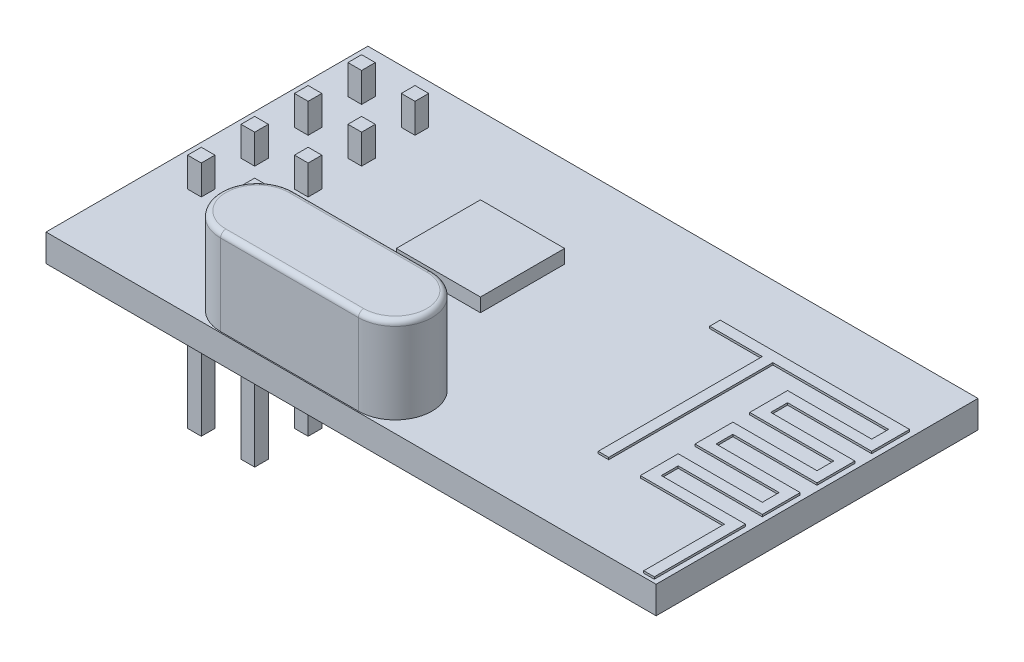
SolidWorks part; units mm, degrees
ref_plane "Front Plane" through (0, 0, 0) normal (0, 0, 1) x (1, 0, 0)
ref_plane "Top Plane" through (0, 0, 0) normal (0, 1, 0) x (1, 0, 0)
ref_plane "Right Plane" through (0, 0, 0) normal (1, 0, 0) x (0, 0, -1)
sketch "Sketch1" plane through (0, 0, 0) normal (0, 1, 0) x (1, 0, 0)
  line L1 (-15.0564, 7.1753) -> (13.9436, 7.1753)
  line L2 (-15.0564, 7.1753) -> (-15.0564, -8.1247)
  line L3 (-15.0564, -8.1247) -> (13.9436, -8.1247)
  line L4 (13.9436, 7.1753) -> (13.9436, -8.1247)
  dimension "D1" = 15.3
  dimension "D2" = 29
extrude "Boss-Extrude1" add sketch "Sketch1" along normal blind 1.3
sketch "Sketch2" plane through (0, 1.3, 0) normal (0, 1, 0) x (1, 0, 0)
  line L0 (-6.8064, -6.3247) -> (-0.2564, -6.3247) construction
  line L1 (-6.8064, -4.5747) -> (-0.2564, -4.5747)
  line L2 (-6.8064, -8.0747) -> (-0.2564, -8.0747)
  line L3 (-15.0564, 7.1753) -> (-15.0564, -8.1247) construction
  line L4 (-15.0564, -8.1247) -> (13.9436, -8.1247) construction
  arc A0 (-6.8064, -4.5747) -> (-6.8064, -8.0747) centre (-6.8064, -6.3247) ccw
  arc A1 (-0.2564, -8.0747) -> (-0.2564, -4.5747) centre (-0.2564, -6.3247) ccw
  point P2 (-3.5314, -6.3247)
  dimension "D1" = 3.5
  dimension "D2" = 6.55
  dimension "D3" = 8.25
  dimension "D4" = 1.8
extrude "Boss-Extrude2" add sketch "Sketch2" along normal blind 4.1
sketch "Sketch3" plane through (0, 1.3, 0) normal (0, 1, 0) x (1, 0, 0)
  line L0 (-15.0564, 7.1753) -> (-15.0564, -8.1247) construction
  line L1 (-13.4564, 5.2753) -> (-12.8064, 5.2753)
  line L2 (-13.4564, 5.2753) -> (-13.4564, 4.6253)
  line L3 (-13.4564, 4.6253) -> (-12.8064, 4.6253)
  line L4 (-12.8064, 5.2753) -> (-12.8064, 4.6253)
  line L5 (13.9436, 7.1753) -> (-15.0564, 7.1753) construction
  line L6 (-10.9164, 5.2753) -> (-10.9164, 4.6253)
  line L7 (-10.9164, 5.2753) -> (-10.2664, 5.2753)
  line L8 (-10.2664, 5.2753) -> (-10.2664, 4.6253)
  line L9 (-10.9164, 4.6253) -> (-10.2664, 4.6253)
  line L10 (-10.9164, 2.7353) -> (-10.9164, 2.0853)
  line L11 (-10.9164, 2.7353) -> (-10.2664, 2.7353)
  line L12 (-10.2664, 2.7353) -> (-10.2664, 2.0853)
  line L13 (-10.9164, 2.0853) -> (-10.2664, 2.0853)
  line L14 (-10.9164, 0.1953) -> (-10.9164, -0.4547)
  line L15 (-10.9164, 0.1953) -> (-10.2664, 0.1953)
  line L16 (-10.2664, 0.1953) -> (-10.2664, -0.4547)
  line L17 (-10.9164, -0.4547) -> (-10.2664, -0.4547)
  line L18 (-10.9164, -2.3447) -> (-10.9164, -2.9947)
  line L19 (-10.9164, -2.3447) -> (-10.2664, -2.3447)
  line L20 (-10.2664, -2.3447) -> (-10.2664, -2.9947)
  line L21 (-10.9164, -2.9947) -> (-10.2664, -2.9947)
  line L22 (-13.4564, 2.7353) -> (-13.4564, 2.0853)
  line L23 (-13.4564, 2.7353) -> (-12.8064, 2.7353)
  line L24 (-12.8064, 2.7353) -> (-12.8064, 2.0853)
  line L25 (-13.4564, 2.0853) -> (-12.8064, 2.0853)
  line L26 (-13.4564, 0.1953) -> (-13.4564, -0.4547)
  line L27 (-13.4564, 0.1953) -> (-12.8064, 0.1953)
  line L28 (-12.8064, 0.1953) -> (-12.8064, -0.4547)
  line L29 (-13.4564, -0.4547) -> (-12.8064, -0.4547)
  line L30 (-13.4564, -2.3447) -> (-13.4564, -2.9947)
  line L31 (-13.4564, -2.3447) -> (-12.8064, -2.3447)
  line L32 (-12.8064, -2.3447) -> (-12.8064, -2.9947)
  line L33 (-13.4564, -2.9947) -> (-12.8064, -2.9947)
  dimension "D1" = 0.65
  dimension "D2" = 0.65
  dimension "D3" = 1.6
  dimension "D4" = 1.9
  dimension "D5" = 2
  dimension "D6" = 4
extrude "Boss-Extrude3" add sketch "Sketch3" along normal blind 1.4 and the other way blind 10
sketch "Sketch4" plane through (0, 0, 0) normal (0, -1, 0) x (1, 0, 0)
  line L0 (-13.4564, 2.3447) -> (-13.4564, 2.9947) construction
  line L1 (-14.3564, 3.8947) -> (-9.3664, 3.8947)
  line L2 (-14.3564, 3.8947) -> (-14.3564, -6.1753)
  line L3 (-14.3564, -6.1753) -> (-9.3664, -6.1753)
  line L4 (-9.3664, 3.8947) -> (-9.3664, -6.1753)
  line L5 (-10.2664, 2.9947) -> (-10.2664, 2.3447) construction
  line L6 (-10.9164, 2.9947) -> (-10.2664, 2.9947) construction
  line L7 (-10.2664, -5.2753) -> (-10.9164, -5.2753) construction
  dimension "D1" = 0.9
  dimension "D2" = 0.9
  dimension "D3" = 0.9
  dimension "D4" = 0.9
extrude "Boss-Extrude4" add sketch "Sketch4" along normal blind 2.54
sketch "Sketch5" plane through (0, 1.3, 0) normal (0, 1, 0) x (1, 0, 0)
  line L0 (-15.0564, 7.1753) -> (-15.0564, -8.1247) construction
  line L1 (-5.4064, 2.8753) -> (-1.4064, 2.8753)
  line L2 (-5.4064, 2.8753) -> (-5.4064, -1.1247)
  line L3 (-5.4064, -1.1247) -> (-1.4064, -1.1247)
  line L4 (-1.4064, 2.8753) -> (-1.4064, -1.1247)
  line L5 (13.9436, 7.1753) -> (-15.0564, 7.1753) construction
  dimension "D1" = 4
  dimension "D2" = 4
  dimension "D3" = 9.65
  dimension "D4" = 4.3
extrude "Boss-Extrude5" add sketch "Sketch5" along normal blind 0.65
fillet "Fillet1" radius 0.25 4 edges at (-3.5314, 5.4, 4.5747) (1.4936, 5.4, 6.3247) (-3.5314, 5.4, 8.0747) (-8.5564, 5.4, 6.3247)
chamfer "Chamfer1" distance 0.15 angle 45 32 edges at (-10.9164, -8.7, 2.6697) (-10.5914, -8.7, 2.9947) (-10.2664, -8.7, 2.6697) (-10.5914, -8.7, 2.3447) (-13.4564, -8.7, 2.6697) (-13.1314, -8.7, 2.9947) (-12.8064, -8.7, 2.6697) (-13.1314, -8.7, 2.3447) (-10.9164, -8.7, 0.1297) (-10.5914, -8.7, 0.4547) (-10.2664, -8.7, 0.1297) (-10.5914, -8.7, -0.1953) (-10.9164, -8.7, -2.4103) (-10.5914, -8.7, -2.0853) (-10.2664, -8.7, -2.4103) (-10.5914, -8.7, -2.7353) (-13.4564, -8.7, 0.1297) (-13.1314, -8.7, 0.4547) (-12.8064, -8.7, 0.1297) (-13.1314, -8.7, -0.1953) (-13.4564, -8.7, -2.4103) (-13.1314, -8.7, -2.0853) (-12.8064, -8.7, -2.4103) (-13.1314, -8.7, -2.7353) (-10.9164, -8.7, -4.9503) (-10.5914, -8.7, -4.6253) (-10.2664, -8.7, -4.9503) (-10.5914, -8.7, -5.2753) (-13.1314, -8.7, -4.6253) (-12.8064, -8.7, -4.9503) (-13.1314, -8.7, -5.2753) (-13.4564, -8.7, -4.9503)
sketch "Sketch6" plane through (0, 1.3, 0) normal (0, 1, 0) x (1, 0, 0)
  line L0 (4.6936, 4.1733) -> (13.6936, 4.1733)
  line L1 (13.6936, 4.1733) -> (13.6936, 2.3733)
  line L2 (13.6936, 2.3733) -> (9.6936, 2.3733)
  line L3 (9.6936, 2.3733) -> (9.6936, 1.5733)
  line L4 (9.6936, 1.5733) -> (13.6936, 1.5733)
  line L5 (13.6936, 1.5733) -> (13.6936, -0.2267)
  line L6 (13.6936, -0.2267) -> (9.6936, -0.2267)
  line L7 (9.6936, -0.2267) -> (9.6936, -1.0267)
  line L8 (9.6936, -1.0267) -> (13.6936, -1.0267)
  line L9 (13.6936, -1.0267) -> (13.6936, -2.8267)
  line L10 (13.6936, -2.8267) -> (9.6936, -2.8267)
  line L11 (9.6936, -2.8267) -> (9.6936, -3.6267)
  line L12 (9.6936, -3.6267) -> (13.6936, -3.6267)
  line L13 (13.6936, -3.6267) -> (13.6936, -7.9624)
  line L14 (13.6936, -7.9624) -> (13.1936, -7.9624)
  line L15 (13.1936, -7.9624) -> (13.1936, -4.1267)
  line L16 (13.1936, -4.1267) -> (9.1936, -4.1267)
  line L17 (9.1936, -4.1267) -> (9.1936, -2.3267)
  line L18 (9.1936, -2.3267) -> (13.1936, -2.3267)
  line L19 (13.1936, -2.3267) -> (13.1936, -1.5267)
  line L20 (13.1936, -1.5267) -> (9.1936, -1.5267)
  line L21 (9.1936, -1.5267) -> (9.1936, 0.2733)
  line L22 (9.1936, 0.2733) -> (13.1936, 0.2733)
  line L23 (13.1936, 0.2733) -> (13.1936, 1.0733)
  line L24 (13.1936, 1.0733) -> (9.1936, 1.0733)
  line L25 (9.1936, 1.0733) -> (9.1936, 2.8733)
  line L26 (9.1936, 2.8733) -> (13.1936, 2.8733)
  line L27 (13.1936, 2.8733) -> (13.1936, 3.6733)
  line L28 (13.1936, 3.6733) -> (7.6936, 3.6733)
  line L29 (7.6936, 3.6733) -> (7.6936, -4.1267)
  line L30 (7.6936, -4.1267) -> (7.1936, -4.1267)
  line L31 (7.1936, -4.1267) -> (7.1936, 3.6719)
  line L32 (7.1936, 3.6719) -> (4.6936, 3.6719)
  line L33 (4.6936, 3.6719) -> (4.6936, 4.1733)
  line L34 (13.9436, -8.1247) -> (13.9436, 7.1753) construction
  dimension "D1" = 0.5
  dimension "D2" = 0.5
  dimension "D3" = 0.5
  dimension "D4" = 0.5
  dimension "D5" = 0.5
  dimension "D6" = 0.5
  dimension "D7" = 0.5
  dimension "D8" = 0.5
  dimension "D9" = 0.5
  dimension "D10" = 0.5
  dimension "D11" = 0.5
  dimension "D12" = 0.5
  dimension "D13" = 0.5
  dimension "D14" = 0.5
  dimension "D15" = 0.5
  dimension "D16" = 0.25
  dimension "D17" = 1.5
  dimension "D18" = 0.8
  dimension "D19" = 0.8
  dimension "D20" = 0.8
  dimension "D21" = 0.8
  dimension "D22" = 0.8
  dimension "D23" = 0.8
  dimension "D24" = 4.5
  dimension "D25" = 9
extrude "Boss-Extrude6" add sketch "Sketch6" along normal blind 0.1
